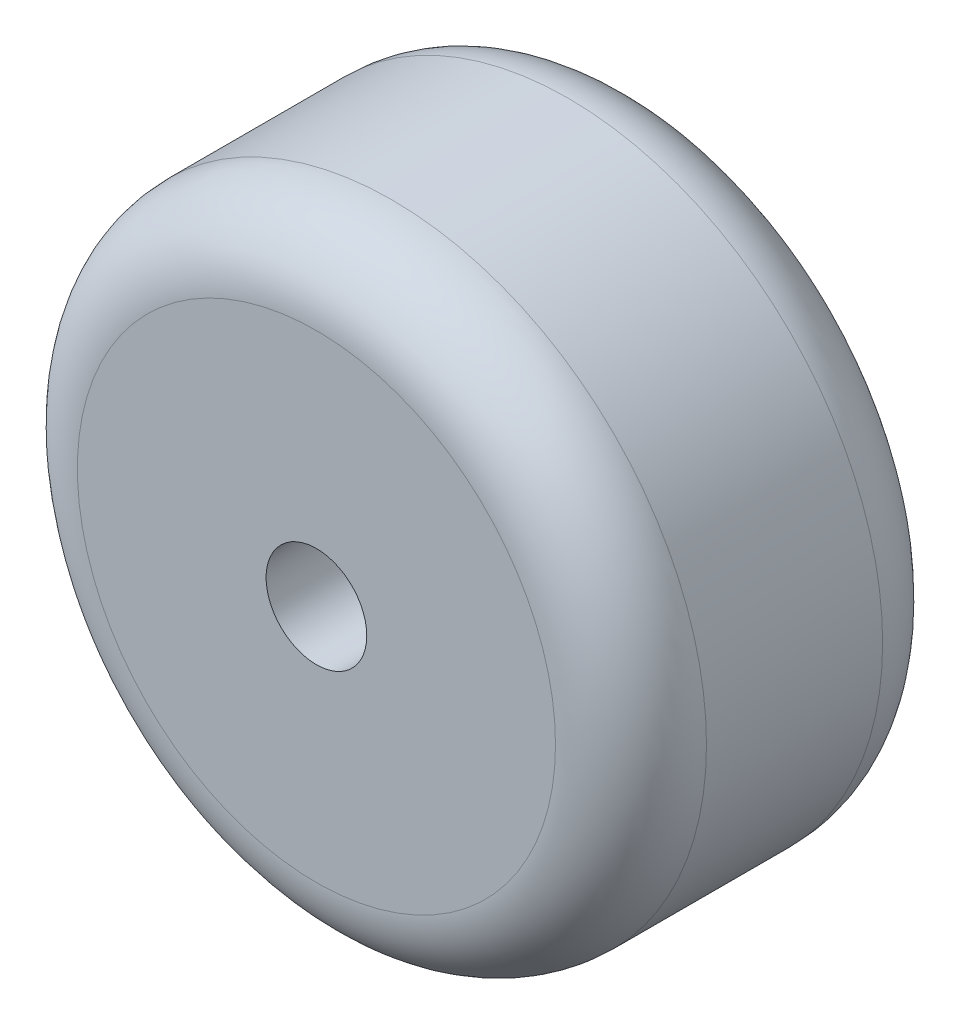
SolidWorks part; units mm, degrees
ref_plane "Front Plane" through (0, 0, 0) normal (0, 0, 1) x (1, 0, 0)
ref_plane "Top Plane" through (0, 0, 0) normal (0, 1, 0) x (1, 0, 0)
ref_plane "Right Plane" through (0, 0, 0) normal (1, 0, 0) x (0, 0, -1)
sketch "Sketch1" plane through (0, 0, 0) normal (0, 1, 0) x (1, 0, 0)
  line L0 (48.5115, 0) -> (-45.3166, 0) construction
  line L1 (0, 26.1054) -> (0, -28.0391) construction
  line L3 (0, -6.5) -> (9.5, -6.5)
  line L4 (0, -6.5) -> (0, 6.5)
  line L5 (0, 6.5) -> (9.5, 6.5)
  line L6 (12.5, -3.5) -> (12.5, 3.5)
  arc A0 (12.5, -3.5) -> (9.5, -6.5) centre (9.5, -3.5) cw
  arc A1 (12.5, 3.5) -> (9.5, 6.5) centre (9.5, 3.5) ccw
  dimension "D4" = 3
  dimension "D1" = 6.5
  dimension "D2" = 6.5
  dimension "D3" = 12.5
revolve "Revolve1" add sketch "Sketch1" angle 360 about L4
sketch "Sketch2" plane through (0, 0, 6.5) normal (0, 0, 1) x (1, 0, 0)
  circle A0 centre (0, 0) radius 2
  dimension "D1" = 4
extrude "Cut-Extrude1" cut sketch "Sketch2" against normal through all both and the other way through all
